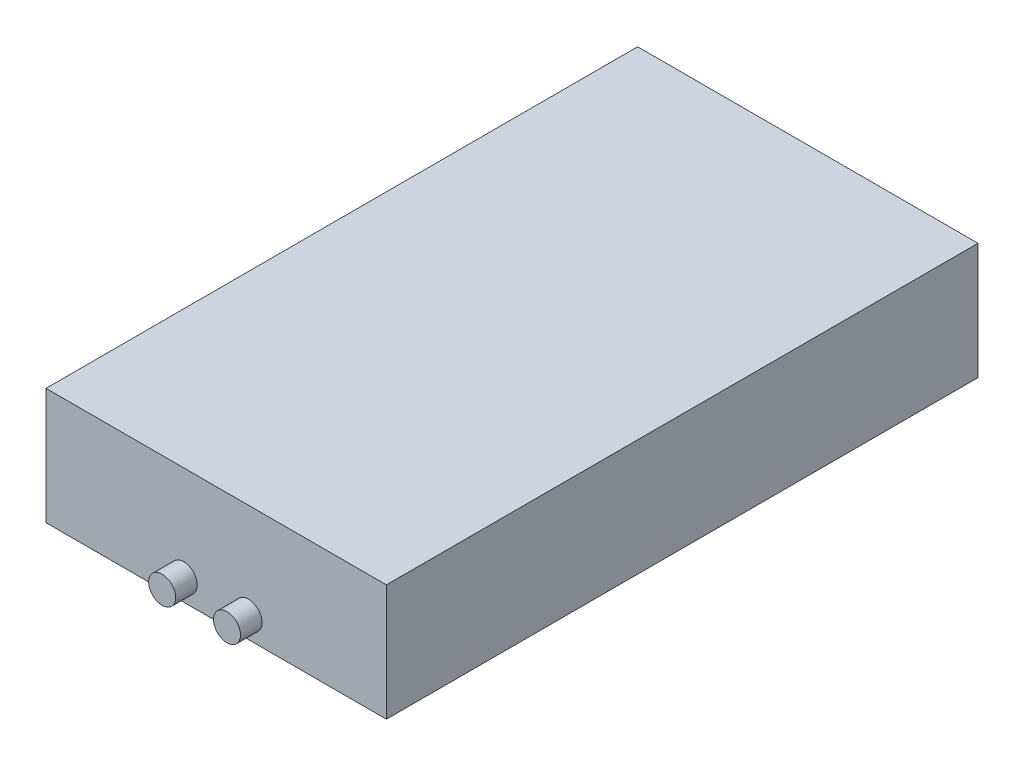
SolidWorks part; units mm, degrees
ref_plane "前视基准面" through (0, 0, 0) normal (0, 0, 1) x (1, 0, 0)
ref_plane "上视基准面" through (0, 0, 0) normal (0, 1, 0) x (1, 0, 0)
ref_plane "右视基准面" through (0, 0, 0) normal (1, 0, 0) x (0, 0, -1)
sketch "草图1" plane through (0, 0, 0) normal (0, 0, 1) x (1, 0, 0)
  line L0 (31.5, 10.77) -> (-31.5, -10.77) construction
  line L1 (-31.5, 10.77) -> (31.5, 10.77)
  line L2 (-31.5, 10.77) -> (-31.5, -10.77)
  line L3 (-31.5, -10.77) -> (31.5, -10.77)
  line L4 (31.5, 10.77) -> (31.5, -10.77)
  dimension "D1" = 63
  dimension "D2" = 21.54
extrude "凸台-拉伸1" add sketch "草图1" along normal blind 109.5
hole_wizard "M2 螺纹孔1" positions "草图3" profile "草图2" tap size "M2" standard "GB"
sketch "草图3" plane through (0, -10.77, 0) normal (0, -1, 0) x (-1, 0, 0)
  line L0 (0, 0) -> (0, -54.2573) construction
  line L1 (31.5, 0) -> (-31.5, 0) construction
  line L2 (31.5, -109.5) -> (-31.5, -109.5) construction
  point P9 (7, -105.2)
  point P14 (-7, -105.2)
  point P17 (-22.3098, -30.7625)
  point P20 (22.3098, -30.7625)
  dimension "D1" = 4.3
  dimension "D2" = 14
  dimension "D3" = 80
sketch "草图2" plane through (-7, -10.77, 105.2) normal (1, 0, 0) x (0, 0, -1)
  line L0 (0, 0) -> (0, 5.6807)
  line L1 (0, 5.6807) -> (0.8, 5.2)
  line L2 (0.8, 5.2) -> (0.8, 0)
  line L5 (0.8, 0) -> (0, 0)
  line L10 (0, 5.6807) -> (-0.8, 5.2) construction
  line L11 (0, -6.35) -> (0, 107.95) construction
  dimension "螺纹孔钻头直径" = 1.6
  dimension "螺纹孔钻头深度" = 5.2
  dimension "导头角度" = 118
cosmetic thread "孔螺蚊线1" parameters "D1"=4, "D2"=2
cosmetic thread "孔螺蚊线2" parameters "D1"=4, "D2"=2
cosmetic thread "孔螺蚊线3" parameters "D1"=4, "D2"=2
cosmetic thread "孔螺蚊线4" parameters "D1"=4, "D2"=2
sketch "草图4" plane through (0, 0, 109.5) normal (0, 0, 1) x (1, 0, 0)
  line L0 (0, -10.77) -> (0, 7.2338) construction
  line L1 (-31.5, -10.77) -> (31.5, -10.77) construction
  line L2 (0, 7.2338) -> (0, -14.4934) construction
  circle A0 centre (-6, -6.77) radius 2.5
  circle A1 centre (6, -6.77) radius 2.5
  dimension "D1" = 5
  dimension "D2" = 4
  dimension "D3" = 6
extrude "凸台-拉伸2" add sketch "草图4" along normal blind 4
sketch "草图5" plane through (0, 0, 0) normal (0, 0, -1) x (-1, 0, 0)
  line L0 (0, -10.77) -> (0, 10.77) construction
  line L1 (31.5, -10.77) -> (-31.5, -10.77) construction
  line L2 (-31.5, 10.77) -> (31.5, 10.77) construction
  circle A0 centre (0, 0) radius 7.4143
  circle A1 centre (0, 0) radius 4.8814
extrude "切除-拉伸1" cut sketch "草图5" against normal blind 2
